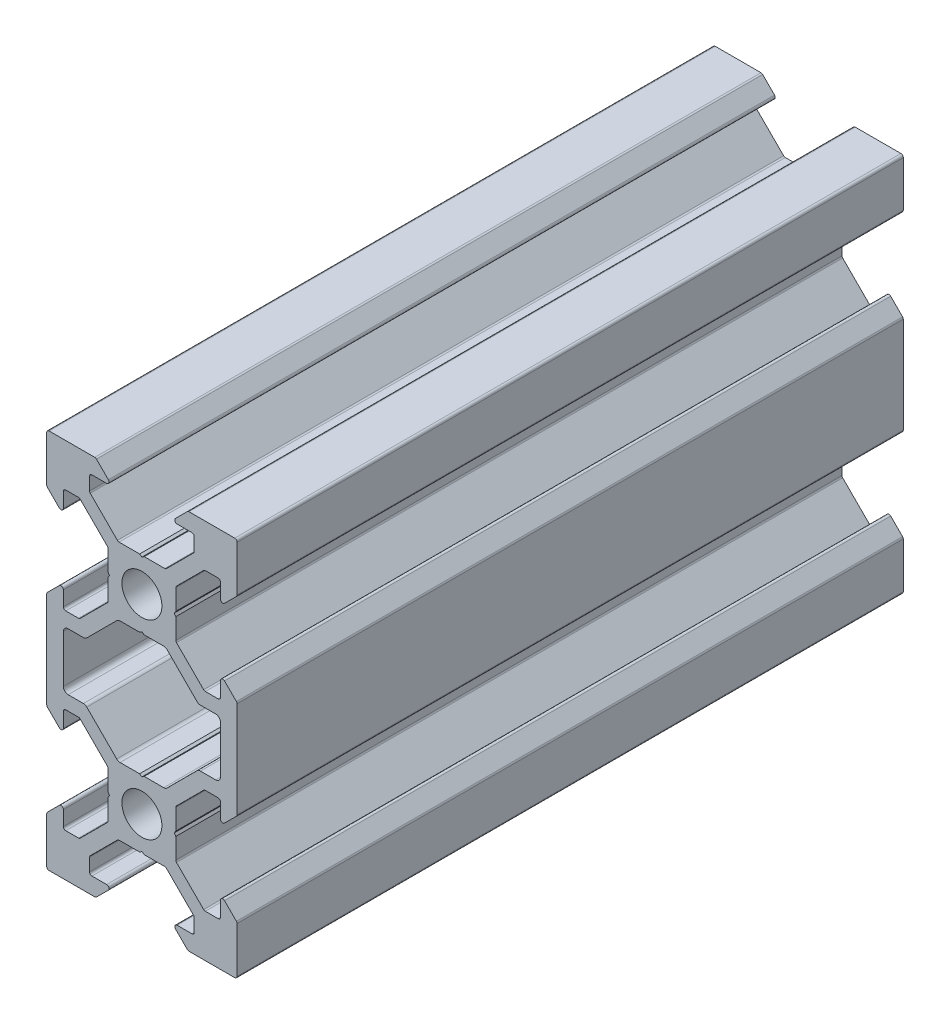
SolidWorks part; units mm, degrees
ref_plane "Front Plane" through (0, 0, 0) normal (0, 0, 1) x (1, 0, 0)
ref_plane "Top Plane" through (0, 0, 0) normal (0, 1, 0) x (1, 0, 0)
ref_plane "Right Plane" through (0, 0, 0) normal (1, 0, 0) x (0, 0, -1)
sketch "Sketch1" plane through (0, 0, 0) normal (0, 0, 1) x (1, 0, 0)
  line L0 (3.5607, 3.5607) -> (10.6317, 10.6317) construction
  line L1 (2.5, -3.5607) -> (-2.5, -3.5607)
  line L2 (3.5607, -2.5) -> (3.5607, 2.5)
  line L3 (2.5, 3.5607) -> (-2.5, 3.5607)
  line L4 (-3.5607, -2.5) -> (-3.5607, 2.5)
  line L5 (3.5607, -3.5607) -> (-3.5607, 3.5607) construction
  line L6 (3.5607, 3.5607) -> (-3.5607, -3.5607) construction
  line L7 (2.5, 3.5607) -> (5.5, 6.5607)
  line L8 (5.5, 6.5607) -> (5.5, 8.2521)
  line L9 (5.5, 8.2521) -> (3.1, 8.2521)
  line L10 (3.1, 8.2521) -> (4.8479, 10)
  line L11 (4.8479, 10) -> (10, 10)
  line L12 (3.5607, 2.5) -> (6.5607, 5.5)
  line L13 (6.5607, 5.5) -> (8.2521, 5.5)
  line L14 (8.2521, 5.5) -> (8.2521, 3.1)
  line L15 (8.2521, 3.1) -> (10, 4.8479)
  line L16 (10, 4.8479) -> (10, 10)
  line L17 (0, -55) -> (0, 55) construction
  line L18 (-3.5607, 3.5607) -> (-10.6317, 10.6317) construction
  line L19 (-10, 4.8479) -> (-10, 10)
  line L20 (-8.2521, 3.1) -> (-10, 4.8479)
  line L21 (-8.2521, 5.5) -> (-8.2521, 3.1)
  line L22 (-6.5607, 5.5) -> (-8.2521, 5.5)
  line L23 (-3.5607, 2.5) -> (-6.5607, 5.5)
  line L24 (-4.8479, 10) -> (-10, 10)
  line L25 (-3.1, 8.2521) -> (-4.8479, 10)
  line L26 (-5.5, 8.2521) -> (-3.1, 8.2521)
  line L27 (-5.5, 6.5607) -> (-5.5, 8.2521)
  line L28 (-2.5, 3.5607) -> (-5.5, 6.5607)
  line L29 (-8.2521, -7) -> (-5.9393, -7)
  line L30 (55, 0) -> (-55, 0) construction
  line L31 (-3.5607, -3.5607) -> (-10.6317, -10.6317) construction
  line L32 (3.5607, -3.5607) -> (10.6317, -10.6317) construction
  line L33 (-2.5, -3.5607) -> (-5.5, -6.5607)
  line L34 (-5.5, -6.5607) -> (-5.9393, -7)
  line L35 (5.5, -6.5607) -> (5.9393, -7)
  line L36 (8.2521, -7) -> (5.9393, -7)
  line L37 (-12.2633, -10) -> (14.5346, -10) construction
  line L38 (-3.5607, -2.5) -> (-6.5607, -5.5)
  line L39 (-6.5607, -5.5) -> (-8.2521, -5.5)
  line L40 (-8.2521, -5.5) -> (-8.2521, -3.1)
  line L41 (-8.2521, -3.1) -> (-10, -4.8479)
  line L42 (-10, -4.8479) -> (-10, -7)
  line L43 (10, -4.8479) -> (10, -7)
  line L44 (8.2521, -3.1) -> (10, -4.8479)
  line L45 (8.2521, -5.5) -> (8.2521, -3.1)
  line L46 (6.5607, -5.5) -> (8.2521, -5.5)
  line L47 (3.5607, -2.5) -> (6.5607, -5.5)
  line L48 (-3.5607, -23.5607) -> (-10.6317, -30.6317) construction
  line L49 (3.5607, -23.5607) -> (-3.5607, -16.4393) construction
  line L50 (3.5607, -16.4393) -> (-3.5607, -23.5607) construction
  line L51 (3.5607, -23.5607) -> (10.6317, -30.6317) construction
  line L52 (2.5, -3.5607) -> (5.5, -6.5607)
  line L53 (2.5, -16.4393) -> (5.5, -13.4393)
  line L54 (3.5607, -17.5) -> (6.5607, -14.5)
  line L55 (6.5607, -14.5) -> (8.2521, -14.5)
  line L56 (8.2521, -14.5) -> (8.2521, -16.9)
  line L57 (8.2521, -16.9) -> (10, -15.1521)
  line L58 (10, -15.1521) -> (10, -13)
  line L59 (-10, -15.1521) -> (-10, -13)
  line L60 (-8.2521, -16.9) -> (-10, -15.1521)
  line L61 (-8.2521, -14.5) -> (-8.2521, -16.9)
  line L62 (-6.5607, -14.5) -> (-8.2521, -14.5)
  line L63 (-3.5607, -17.5) -> (-6.5607, -14.5)
  line L64 (8.2521, -13) -> (5.9393, -13)
  line L65 (5.5, -13.4393) -> (5.9393, -13)
  line L66 (-5.5, -13.4393) -> (-5.9393, -13)
  line L67 (-2.5, -16.4393) -> (-5.5, -13.4393)
  line L68 (-8.2521, -13) -> (-5.9393, -13)
  line L69 (-2.5, -23.5607) -> (-5.5, -26.5607)
  line L70 (-5.5, -26.5607) -> (-5.5, -28.2521)
  line L71 (-5.5, -28.2521) -> (-3.1, -28.2521)
  line L72 (-3.1, -28.2521) -> (-4.8479, -30)
  line L73 (-4.8479, -30) -> (-10, -30)
  line L74 (-3.5607, -22.5) -> (-6.5607, -25.5)
  line L75 (-6.5607, -25.5) -> (-8.2521, -25.5)
  line L76 (-8.2521, -25.5) -> (-8.2521, -23.1)
  line L77 (-8.2521, -23.1) -> (-10, -24.8479)
  line L78 (-10, -24.8479) -> (-10, -30)
  line L79 (10, -24.8479) -> (10, -30)
  line L80 (8.2521, -23.1) -> (10, -24.8479)
  line L81 (8.2521, -25.5) -> (8.2521, -23.1)
  line L82 (6.5607, -25.5) -> (8.2521, -25.5)
  line L83 (3.5607, -22.5) -> (6.5607, -25.5)
  line L84 (4.8479, -30) -> (10, -30)
  line L85 (3.1, -28.2521) -> (4.8479, -30)
  line L86 (5.5, -28.2521) -> (3.1, -28.2521)
  line L87 (5.5, -26.5607) -> (5.5, -28.2521)
  line L88 (2.5, -23.5607) -> (5.5, -26.5607)
  line L89 (-3.5607, -17.5) -> (-3.5607, -22.5)
  line L90 (2.5, -23.5607) -> (-2.5, -23.5607)
  line L91 (3.5607, -17.5) -> (3.5607, -22.5)
  line L92 (2.5, -16.4393) -> (-2.5, -16.4393)
  line L93 (-10, -7) -> (-10, -13)
  line L94 (-8.2521, -13) -> (-8.2521, -7)
  line L95 (8.2521, -13) -> (8.2521, -7)
  line L96 (10, -7) -> (10, -13)
  circle A0 centre (0, 0) radius 2.1
  circle A1 centre (0, -20) radius 2.1
  point P0 (0, 0)
  point P102 (0, -20)
  dimension "D10" = 4.2
  dimension "D11" = 4.2
  dimension "D1" = 1.5
  dimension "D2" = 10
  dimension "D3" = 20
  dimension "D4" = 6.2
  dimension "D5" = 11
  dimension "D6" = 45
  dimension "D7" = 1.5
  dimension "D8" = 10
  dimension "D9" = 5
extrude "Boss-Extrude1" add sketch "Sketch1" along normal blind 70
fillet "Fillet1" radius 0.25 64 edges at (5.5, 6.5607, 35) (5.5, 8.2521, 35) (3.1, 8.2521, 35) (4.8479, 10, 35) (10, 10, 35) (10, 4.8479, 35) (8.2521, 3.1, 35) (8.2521, 5.5, 35) (6.5607, 5.5, 35) (3.5607, 2.5, 35) (3.5607, -2.5, 35) (6.5607, -5.5, 35) (8.2521, -5.5, 35) (8.2521, -3.1, 35) (10, -4.8479, 35) (10, -15.1521, 35) (8.2521, -16.9, 35) (8.2521, -14.5, 35) (6.5607, -14.5, 35) (3.5607, -17.5, 35) (3.5607, -22.5, 35) (6.5607, -25.5, 35) (8.2521, -25.5, 35) (8.2521, -23.1, 35) (10, -24.8479, 35) (10, -30, 35) (4.8479, -30, 35) (3.1, -28.2521, 35) (5.5, -28.2521, 35) (5.5, -26.5607, 35) (2.5, -23.5607, 35) (-2.5, -23.5607, 35) (-5.5, -26.5607, 35) (-5.5, -28.2521, 35) (-3.1, -28.2521, 35) (-4.8479, -30, 35) (-10, -30, 35) (-10, -24.8479, 35) (-8.2521, -23.1, 35) (-8.2521, -25.5, 35) (-6.5607, -25.5, 35) (-3.5607, -22.5, 35) (-3.5607, -17.5, 35) (-6.5607, -14.5, 35) (-8.2521, -14.5, 35) (-8.2521, -16.9, 35) (-10, -15.1521, 35) (-10, -4.8479, 35) (-8.2521, -3.1, 35) (-8.2521, -5.5, 35) (-6.5607, -5.5, 35) (-3.5607, -2.5, 35) (-3.5607, 2.5, 35) (-6.5607, 5.5, 35) (-8.2521, 5.5, 35) (-8.2521, 3.1, 35) (-10, 4.8479, 35) (-10, 10, 35) (-4.8479, 10, 35) (-5.5, 8.2521, 35) (-5.5, 6.5607, 35) (-2.5, 3.5607, 35) (2.5, 3.5607, 35) (-3.1, 8.2521, 35)
fillet "Fillet2" radius 0.5 12 edges at (-5.9393, -7, 35) (-8.2521, -7, 35) (-8.2521, -13, 35) (-5.9393, -13, 35) (-2.5, -16.4393, 35) (2.5, -16.4393, 35) (8.2521, -7, 35) (5.9393, -7, 35) (2.5, -3.5607, 35) (-2.5, -3.5607, 35) (5.9393, -13, 35) (8.2521, -13, 35)
sketch "Sketch2" plane through (0, 0, 70) normal (0, 0, 1) x (1, 0, 0)
  line L4 (0, 3.5607) -> (0, 3.1447) construction
  line L5 (2.3964, 3.5607) -> (-2.3964, 3.5607) construction
  line L6 (0, 3.399) -> (-0.2423, 3.5607)
  line L7 (0, 3.399) -> (0.2423, 3.5607)
  line L8 (-0.2423, 3.5607) -> (0.2423, 3.5607)
  line L9 (55, 0) -> (-55, 0) construction
  line L10 (0, -3.5607) -> (0, -3.1447) construction
  line L11 (0, -3.399) -> (0.2423, -3.5607)
  line L12 (0, -3.399) -> (-0.2423, -3.5607)
  line L13 (-0.2423, -3.5607) -> (0.2423, -3.5607)
  line L14 (0, 0) -> (-4.0856, 4.0856) construction
  line L15 (-8.2521, -10) -> (4.1581, -10) construction
  line L16 (-8.2521, -7.5) -> (-8.2521, -12.5) construction
  line L17 (3.5607, 0) -> (3.1447, 0) construction
  line L18 (3.5607, 0.2423) -> (3.5607, -0.2423)
  line L19 (3.399, 0) -> (3.5607, 0.2423)
  line L20 (3.399, 0) -> (3.5607, -0.2423)
  line L21 (-3.5607, 0) -> (-3.1447, 0) construction
  line L22 (-3.5607, 0.2423) -> (-3.5607, -0.2423)
  line L23 (-3.399, 0) -> (-3.5607, -0.2423)
  line L24 (-3.399, 0) -> (-3.5607, 0.2423)
  line L25 (-3.5607, -20) -> (-3.1447, -20) construction
  line L26 (3.5607, -20) -> (3.1447, -20) construction
  line L27 (0, -20) -> (-4.0856, -24.0856) construction
  line L28 (0, -16.4393) -> (0, -16.8553) construction
  line L29 (0, -23.5607) -> (0, -23.1447) construction
  line L30 (-3.399, -20) -> (-3.5607, -20.2423)
  line L31 (-3.399, -20) -> (-3.5607, -19.7577)
  line L32 (-3.5607, -20.2423) -> (-3.5607, -19.7577)
  line L33 (3.399, -20) -> (3.5607, -19.7577)
  line L34 (3.399, -20) -> (3.5607, -20.2423)
  line L35 (3.5607, -20.2423) -> (3.5607, -19.7577)
  line L36 (-0.2423, -16.4393) -> (0.2423, -16.4393)
  line L37 (0, -16.601) -> (-0.2423, -16.4393)
  line L38 (0, -16.601) -> (0.2423, -16.4393)
  line L39 (-0.2423, -23.5607) -> (0.2423, -23.5607)
  line L40 (0, -23.399) -> (0.2423, -23.5607)
  line L41 (0, -23.399) -> (-0.2423, -23.5607)
extrude "Cut-Extrude1" cut sketch "Sketch2" against normal through all
